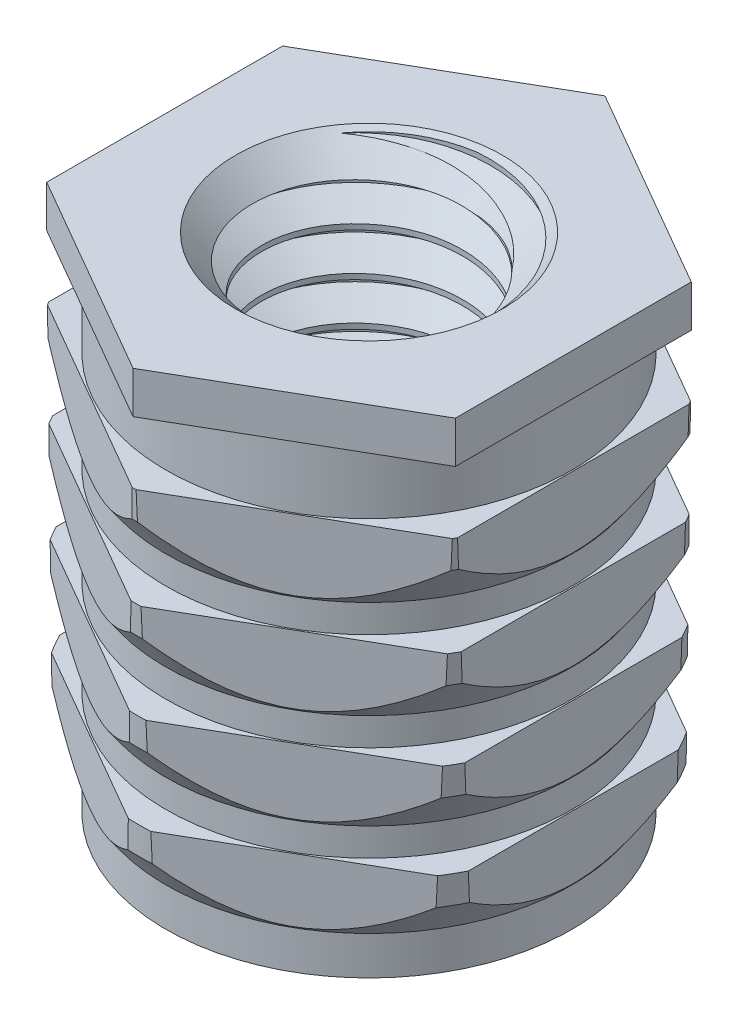
SolidWorks part; units mm, degrees
ref_plane "Front Plane" through (0, 0, 0) normal (0, 0, 1) x (1, 0, 0)
ref_plane "Top Plane" through (0, 0, 0) normal (0, 1, 0) x (1, 0, 0)
ref_plane "Right Plane" through (0, 0, 0) normal (1, 0, 0) x (0, 0, -1)
sketch "Sketch1" plane through (0, 0, 0) normal (0, 1, 0) x (1, 0, 0)
  line L0 (-2.36, 0) -> (2.36, 0) construction
  line L1 (-2.36, 0) -> (-2.375, 0) construction
  line L2 (0, 2.7424) -> (-2.375, 1.3712)
  line L3 (-2.375, 1.3712) -> (-2.375, -1.3712)
  line L4 (-2.375, -1.3712) -> (0, -2.7424)
  line L5 (0, -2.7424) -> (2.375, -1.3712)
  line L6 (2.375, -1.3712) -> (2.375, 1.3712)
  line L7 (2.375, 1.3712) -> (0, 2.7424)
  line L8 (2.36, 0) -> (2.375, 0) construction
  line L9 (-2.7424, 0) -> (-2.375, 0) construction
  circle A0 centre (0, 0) radius 2.36 construction
  circle A1 centre (0, 0) radius 2.375 construction
  circle A2 centre (0, 0) radius 2.7424 construction
  dimension "OD" = 4.72
  dimension "Hex" = 4.75
extrude "Extrude1" add sketch "Sketch1" against normal blind 5.84
sketch "Sketch2" plane through (0, 0, 0) normal (0, 1, 0) x (1, 0, 0)
  circle A2 centre (0, 0) radius 1.5
  point P0 (-1.5, 0)
  dimension "Internal Thread OD" = 3
curve "Helix/Spiral1" pitch 0.5 height 6.8781 turns 13.7562 parameters "Internal Thread Height"=6.8781, "Internal Thread Pitch"=0.5
sketch "Sketch3" plane through (0, 0, 0) normal (0, 0, 1) x (1, 0, 0)
  line L0 (-1.1211, 0.2813) -> (-1.1211, -0.2188) construction
  line L1 (-1.1211, -0.2188) -> (-1.5541, 0.0312) construction
  line L2 (-1.5541, 0.0312) -> (-1.1211, 0.2813) construction
  line L3 (-1.1211, 0.0312) -> (-1.1752, 0.0312) construction
  line L4 (-1.1752, 0.0312) -> (-1.5, 0.0312) construction
  line L5 (-1.5, 0.0312) -> (-1.5541, 0.0312) construction
  line L6 (-1.5, 0.0625) -> (-1.5, 0)
  line L7 (-1.1752, -0.1875) -> (-1.1752, 0.25) construction
  line L11 (-1.5, 0) -> (-1.1482, -0.2031)
  line L12 (-1.1482, -0.2031) -> (-1.1482, 0.2656)
  line L13 (-1.1482, 0.2656) -> (-1.5, 0.0625)
  point P18 (-1.1482, 0.0313)
  dimension "D1" = 0.5
  dimension "D2" = 0.0625
sketch "Sketch4" plane through (0, 0, 0) normal (0, 1, 0) x (-1, 0, 0)
  circle A0 centre (0, 0) radius 1.1752
extrude "Extrude2" cut sketch "Sketch4" against normal through all
chamfer "Chamfer1" distance 0.375 angle 45 2 edges at (0, 0, 1.1752) (0, -5.84, 1.1752)
sweep "Cut-Sweep1" cut profiles "Sketch3" path "Helix/Spiral1"
sketch "Sketch5" plane through (0, 0, 0) normal (0, 0, 1) x (1, 0, 0)
  line L0 (2.7424, 0) -> (-2.7424, 0) construction
  line L1 (-2.36, 0) -> (-2.36, -5.84) construction
  line L2 (-2.36, 0) -> (-2.7424, 0) construction
  line L3 (0, 0) -> (0, -5.84) construction
  line L4 (-2.375, -5.84) -> (0, -5.84) construction
  line L5 (-2.36, -5.84) -> (-2.7424, -5.84)
  line L6 (-2.7424, 0) -> (-2.375, 0) construction
  line L7 (-2.7424, 0) -> (-2.7424, -5.84) construction
  line L8 (-2.7424, -0.4867) -> (-2.649, -5.84) construction
  line L9 (-2.7424, -0.4867) -> (-2.36, -0.4867)
  line L10 (-2.7424, 0) -> (-2.7424, -0.4867)
  line L11 (-2.36, -0.4867) -> (-2.36, -1.2167)
  line L12 (-2.6837, -3.8476) -> (-2.36, -4.31)
  line L13 (-2.36, -5.84) -> (-2.36, -5.3928)
  line L14 (-2.36, -4.31) -> (-2.36, -4.634)
  line L15 (-2.36, -1.2167) -> (-2.7297, -1.2167)
  line L16 (-2.7297, -1.2167) -> (-2.724, -1.5407)
  line L17 (-2.724, -1.5407) -> (-2.36, -2.0606)
  line L18 (-2.36, -4.634) -> (-2.67, -4.634)
  line L19 (-2.7424, 0) -> (-3.1248, 0)
  line L20 (-3.1248, 0) -> (-3.1248, -5.84)
  line L21 (-3.1248, -5.84) -> (-2.7424, -5.84)
  line L22 (-2.36, -2.3847) -> (-2.7093, -2.3847)
  line L23 (-2.36, -2.0606) -> (-2.36, -2.3847)
  line L24 (-2.7093, -2.3847) -> (-2.7036, -2.7087)
  line L25 (-2.7036, -2.7087) -> (-2.36, -3.1995)
  line L26 (-2.36, -3.5236) -> (-2.6894, -3.5236)
  line L27 (-2.6894, -3.5236) -> (-2.6837, -3.8476)
  line L28 (-2.67, -4.634) -> (-2.6644, -4.9581)
  line L29 (-2.36, -3.1995) -> (-2.36, -3.5236)
  line L30 (-2.6644, -4.9581) -> (-2.36, -5.3928)
  dimension "D1" = 0.4867
  dimension "D2" = 1
  dimension "D3" = 1.168
  dimension "D5" = 35
  dimension "D6" = 0.73
revolve "Cut-Revolve1" cut sketch "Sketch5" angle 360 about L3
equation "\"Internal Thread Height@Helix/Spiral1\" = \"Internal Thread Pitch@Helix/Spiral1\" + \"Length@Extrude1\" + 0.5381"
equation "\"D1@Sketch3\" = \"Internal Thread Pitch@Helix/Spiral1\""
equation "\"D2@Sketch3\" = \"D1@Sketch3\" * 1 / 8"
equation "\"D1@Chamfer1\" = \"Internal Thread Pitch@Helix/Spiral1\" * 6 / 8"
equation "\"D1@Sketch5\" = \"Length@Extrude1\"  * 1 / 12"
equation "\"D6@Sketch5\" = \"D1@Sketch5\" * 1.5"
equation "\"D3@Sketch5\" = \"Length@Extrude1\"  * 1 / 5"
